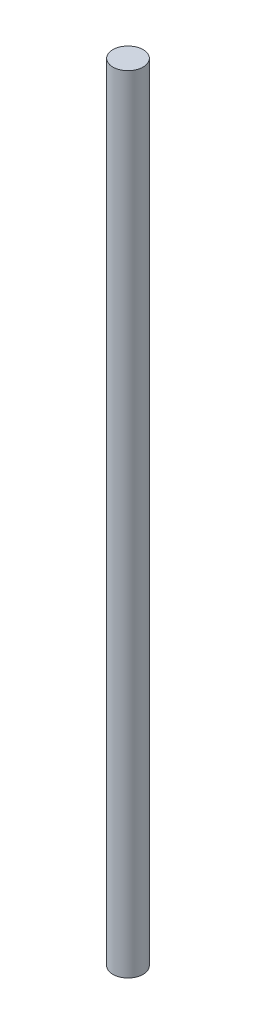
SolidWorks part; units mm, degrees
ref_plane "Plan de face" through (0, 0, 0) normal (0, 0, 1) x (1, 0, 0)
ref_plane "Plan de dessus" through (0, 0, 0) normal (0, 1, 0) x (1, 0, 0)
ref_plane "Plan de droite" through (0, 0, 0) normal (1, 0, 0) x (0, 0, -1)
sketch "Esquisse1" plane through (0, 0, 0) normal (0, 1, 0) x (1, 0, 0)
  circle A0 centre (0, 0) radius 5
  dimension "D1" = 10
extrude "Boss.-Extru.1" add sketch "Esquisse1" along normal blind 260
